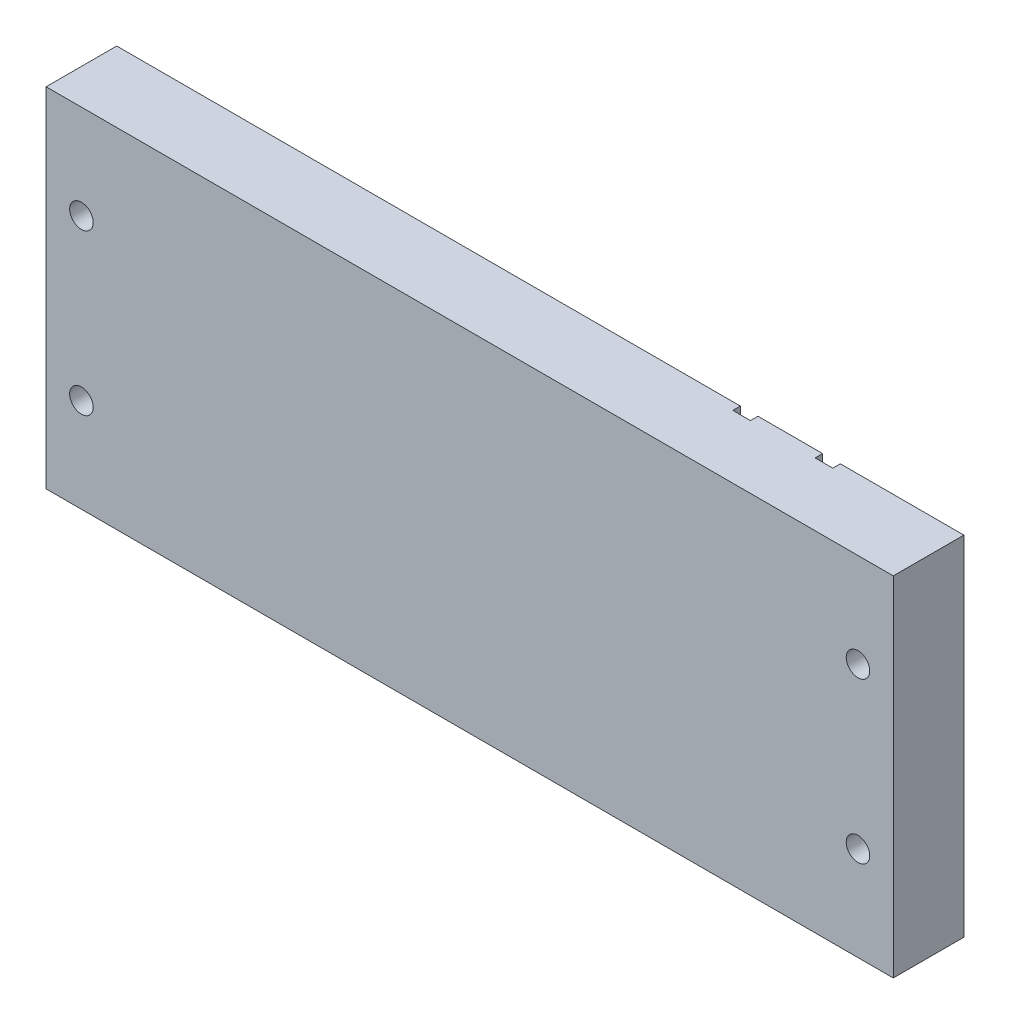
SolidWorks part; units mm, degrees
material "Pine"
ref_plane "Front Plane" through (0, 0, 0) normal (0, 0, 1) x (1, 0, 0)
ref_plane "Top Plane" through (0, 0, 0) normal (0, 1, 0) x (1, 0, 0)
ref_plane "Right Plane" through (0, 0, 0) normal (1, 0, 0) x (0, 0, -1)
sketch3d "3DSketch2"
  line L0 (69.85, 0, -9.525) -> (36.5125, 0, -9.525)
  line L1 (-158.75, 0, -9.525) -> (-158.75, 0, 9.525)
  line L2 (31.75, 0, -9.525) -> (14.2875, 0, -9.525)
  line L3 (69.85, 0, -9.525) -> (69.85, 0, 9.525)
  line L4 (-158.75, 0, 9.525) -> (69.85, 0, 9.525)
  line L5 (-158.75, 0, -9.525) -> (69.85, 0, 9.525) construction
  line L6 (69.85, 0, -9.525) -> (-158.75, 0, 9.525) construction
  line L7 (9.525, 0, -9.525) -> (9.525, 0, -7.493)
  line L8 (14.2875, 0, -9.525) -> (14.2875, 0, -7.493)
  line L9 (9.525, 0, -7.493) -> (14.2875, 0, -7.493)
  line L10 (-158.75, 0, -9.525) -> (9.525, 0, -9.525)
  line L11 (36.5125, 0, -9.525) -> (36.5125, 0, -7.493)
  line L12 (31.75, 0, -9.525) -> (31.75, 0, -7.493)
  line L13 (36.5125, 0, -7.493) -> (31.75, 0, -7.493)
  point P0 (-44.45, 0, 0)
  point P6 (9.525, 0, -9.525)
  point P7 (36.5125, 0, -9.525)
  dimension "D1" = 228.6
  dimension "D2" = 19.05
  dimension "D3" = 33.3375
  dimension "D4" = 60.325
  dimension "D5" = 4.7625
  dimension "D6" = 2.032
extrude "Boss-Extrude2" add sketch "3DSketch2" along direction (0, 1, 0) on the side of the normal mid plane 93.98
hole_wizard "1/4 (0.25) Diameter Hole1" positions "Sketch2" profile "Sketch1" hole size "1/4" standard "Ansi Inch"
sketch "Sketch2" plane through (0, 0, -9.525) normal (0, 0, -1) x (-1, 0, 0)
  line L0 (-9.525, -46.99) -> (158.75, -46.99) construction
  line L1 (158.75, -46.99) -> (158.75, 46.99) construction
  point P1 (149.225, -21.59)
  dimension "D1" = 25.4
  dimension "D2" = 9.525
sketch "Sketch1" plane through (-149.225, -21.59, -9.525) normal (1, 0, 0) x (0, 1, 0)
  line L0 (0, 0) -> (0, 20.9577)
  line L1 (0, 20.9577) -> (3.175, 19.05)
  line L2 (3.175, 19.05) -> (3.175, 0)
  line L5 (3.175, 0) -> (0, 0)
  line L10 (0, 20.9577) -> (-3.175, 19.05) construction
  line L11 (0, -6.35) -> (0, 107.95) construction
  dimension "Hole Dia." = 6.35
  dimension "Hole Depth" = 19.05
  dimension "Drill Angle" = 118
mirror "Mirror1" about plane through (0, 0, 0) normal (0, 1, 0) of "1/4 (0.25) Diameter Hole1"
hole_wizard "1/4 (0.25) Diameter Hole2" positions "Sketch4" profile "Sketch3" hole size "1/4" standard "Ansi Inch"
sketch "Sketch4" plane through (0, 0, -9.525) normal (0, 0, -1) x (-1, 0, 0)
  line L0 (-69.85, -46.99) -> (-69.85, 46.99) construction
  line L1 (-69.85, -46.99) -> (-36.5125, -46.99) construction
  point P0 (-60.325, -21.59)
  dimension "D1" = 9.525
  dimension "D2" = 25.4
sketch "Sketch3" plane through (60.325, -21.59, -9.525) normal (1, 0, 0) x (0, 1, 0)
  line L0 (0, 0) -> (0, 20.9577)
  line L1 (0, 20.9577) -> (3.175, 19.05)
  line L2 (3.175, 19.05) -> (3.175, 0)
  line L5 (3.175, 0) -> (0, 0)
  line L10 (0, 20.9577) -> (-3.175, 19.05) construction
  line L11 (0, -6.35) -> (0, 107.95) construction
  dimension "Hole Dia." = 6.35
  dimension "Hole Depth" = 19.05
  dimension "Drill Angle" = 118
mirror "Mirror2" about plane through (0, 0, 0) normal (0, 1, 0) of "1/4 (0.25) Diameter Hole2"
